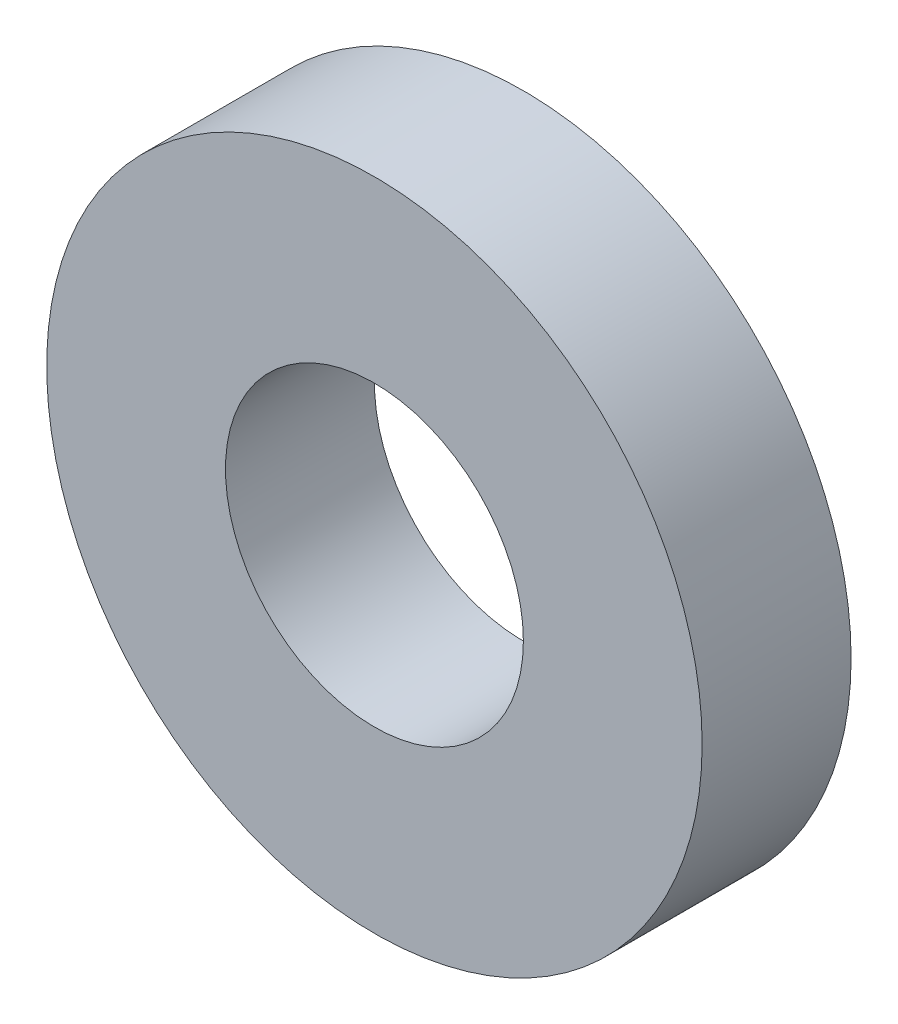
SolidWorks part; units mm, degrees
ref_plane "Front Plane" through (0, 0, 0) normal (0, 0, 1) x (1, 0, 0)
ref_plane "Top Plane" through (0, 0, 0) normal (0, 1, 0) x (1, 0, 0)
ref_plane "Right Plane" through (0, 0, 0) normal (1, 0, 0) x (0, 0, -1)
sketch "Sketch1" plane through (0, 0, 0) normal (0, 0, 1) x (1, 0, 0)
  circle A0 centre (0, 0) radius 6
  circle A1 centre (0, 0) radius 13.2
extrude "Boss-Extrude1" add sketch "Sketch1" along normal blind 6
sketch "Sketch2" plane through (0, 0, 6) normal (0, 0, 1) x (1, 0, 0)
  line L0 (0, 0) -> (0, 15.2) construction
  line L1 (-1.8199, 15.2) -> (0, 0) construction
  line L2 (1.8199, 15.2) -> (0, 0) construction
  line L3 (-1.1225, 12) -> (0.9099, 12)
  arc A0 (-2.8199, 12.8953) -> (2.8199, 12.8953) centre (0, 0) cw
  arc A1 (-1.8199, 10.32) -> (1.8199, 10.32) centre (0, 0) cw
  arc A2 (-2.8199, 12.8953) -> (-1.8199, 10.32) centre (-2.3199, 11.6076) cw
  arc A3 (2.8199, 12.8953) -> (1.8199, 10.32) centre (2.3199, 11.6076) ccw
